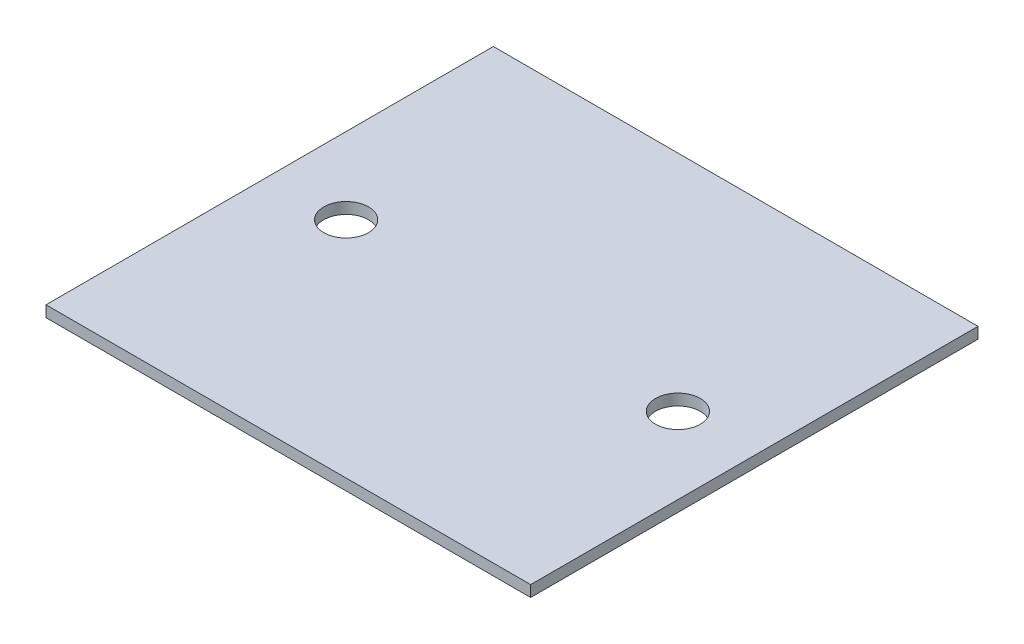
SolidWorks part; units mm, degrees
ref_plane "Front Plane" through (0, 0, 0) normal (0, 0, 1) x (1, 0, 0)
ref_plane "Top Plane" through (0, 0, 0) normal (0, 1, 0) x (1, 0, 0)
ref_plane "Right Plane" through (0, 0, 0) normal (1, 0, 0) x (0, 0, -1)
sketch "Sketch1" plane through (0, 0, 0) normal (0, 1, 0) x (1, 0, 0)
  line L1 (-65, -60) -> (65, -60)
  line L2 (-65, -60) -> (-65, 60)
  line L3 (-65, 60) -> (65, 60)
  line L4 (65, -60) -> (65, 60)
  line L5 (-65, -60) -> (65, 60) construction
  line L6 (-65, 60) -> (65, -60) construction
  point P0 (0, 0)
  dimension "D1" = 130
  dimension "D2" = 120
extrude "Boss-Extrude1" add sketch "Sketch1" along normal blind 3
sketch "Sketch2" plane through (0, 3, 0) normal (0, 1, 0) x (1, 0, 0)
  circle A0 centre (44.5, 0) radius 6
  dimension "D1" = 12
  dimension "D2" = 44.5
extrude "Cut-Extrude1" cut sketch "Sketch2" against normal through all both and the other way through all
mirror "Mirror1" about plane through (0, 0, 0) normal (1, 0, 0) of "Cut-Extrude1"
